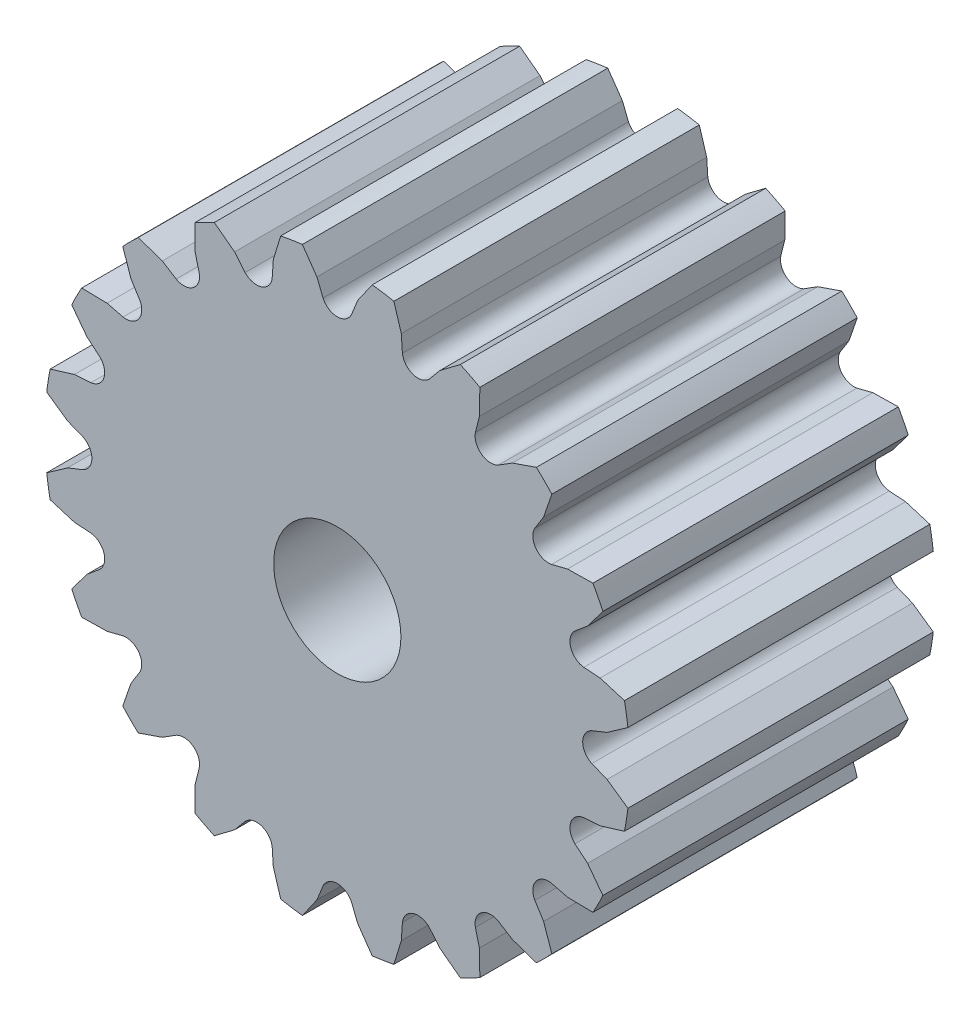
SolidWorks part; units mm, degrees
ref_plane "Plan de face" through (0, 0, 0) normal (0, 0, 1) x (1, 0, 0)
ref_plane "Plan de dessus" through (0, 0, 0) normal (0, 1, 0) x (1, 0, 0)
ref_plane "Plan de droite" through (0, 0, 0) normal (1, 0, 0) x (0, 0, -1)
sketch "Sketch1" plane through (0, 0, 0) normal (0, 0, 1) x (1, 0, 0)
  circle A0 centre (0, 0) radius 11.5
  circle A1 centre (0, 0) radius 2.5
  dimension "D1" = 23
  dimension "D2" = 5
extrude "Boss-Extrude1" add sketch "Sketch1" along normal blind 12
sketch "Sketch2" plane through (0, 0, 12) normal (0, 0, 1) x (1, 0, 0)
  line L1 (0, 11.6) -> (1.5, 11.6)
  line L2 (0, 10.6) -> (0, 11.6) construction
  line L3 (0, 10) -> (0.5593, 10) construction
  line L4 (0, 10) -> (-0.5593, 10) construction
  line L5 (0, 11.6) -> (-1.5, 11.6)
  line L6 (-1.5, 11.6) -> (-0.8, 10.6)
  line L7 (-0.8, 10.6) -> (-0.5593, 10)
  line L8 (-0.8, 10.6) -> (0, 10.6) construction
  line L9 (0, 10.6) -> (0.8, 10.6) construction
  line L10 (1.5, 11.6) -> (0.8, 10.6)
  line L11 (0.8, 10.6) -> (0.5593, 10)
  line L12 (0, 10.6) -> (0, 10) construction
  circle A0 centre (0, 0) radius 11.5 construction
  arc A2 (-0.5593, 10) -> (0.5593, 10) centre (0, 10.2587) ccw
  dimension "D1" = 1
  dimension "D2" = 1.5
  dimension "D3" = 0.8
  dimension "D4" = 10
  dimension "D5" = 0.6
extrude "Cut-Extrude1" cut sketch "Sketch2" against normal blind 12
pattern_circular "CirPattern1" count 20 over 360 about axis through (0, 0, 0) along (0, 0, 1) of "Cut-Extrude1"
